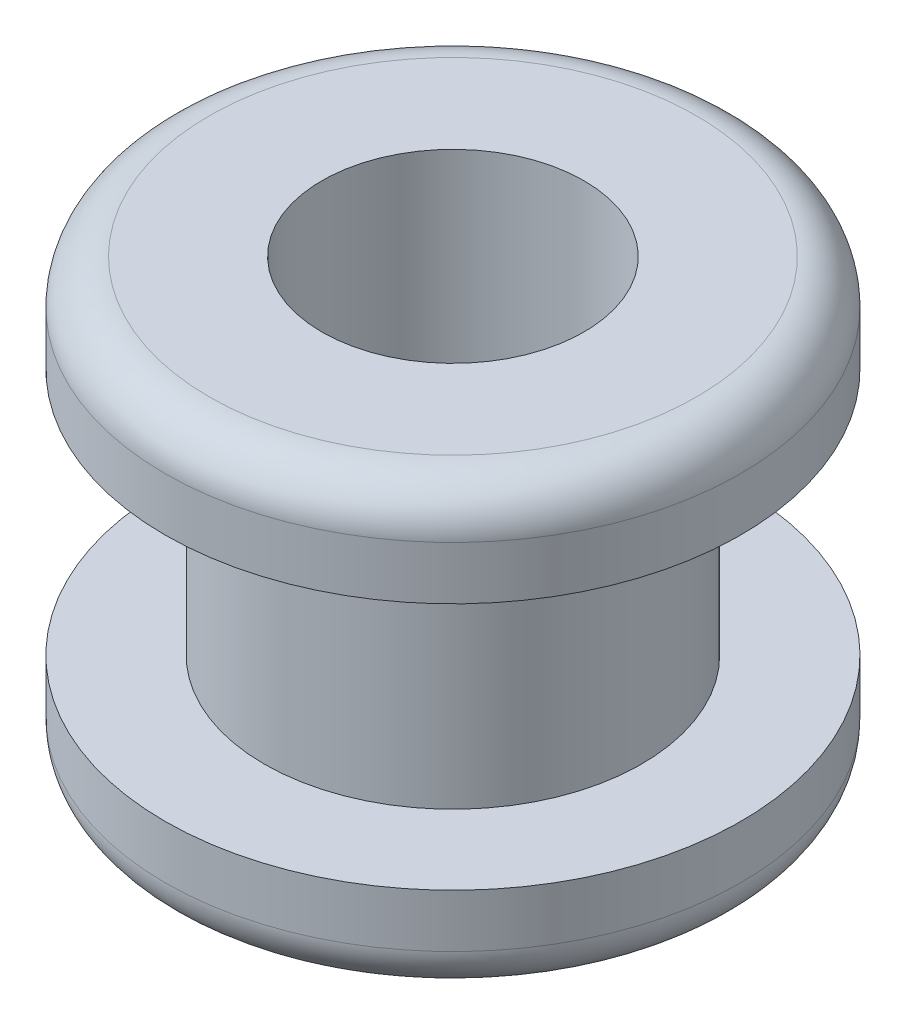
SolidWorks part; units mm, degrees
ref_plane "Ön Düzlem" through (0, 0, 0) normal (0, 0, 1) x (1, 0, 0)
ref_plane "Üst Düzlem" through (0, 0, 0) normal (0, 1, 0) x (1, 0, 0)
ref_plane "Sağ Düzlem" through (0, 0, 0) normal (1, 0, 0) x (0, 0, -1)
sketch "Çizim1" plane through (0, 0, 0) normal (1, 0, 0) x (0, 0, -1)
  line L0 (0, 5) -> (0, 0)
  line L1 (0, 5) -> (-1.27, 5)
  line L2 (1.48, 5) -> (1.48, 0.688) construction
  line L3 (-0.65, 3.9) -> (-0.65, 1.1)
  line L4 (-0.65, 3.9) -> (-1.77, 3.9)
  line L5 (-1.77, 3.9) -> (-1.77, 4.5)
  line L6 (-0.65, 1.1) -> (-1.77, 1.1)
  line L7 (-1.77, 1.1) -> (-1.77, 0.5)
  line L8 (0, 0) -> (-1.27, 0)
  arc A0 (-1.27, 5) -> (-1.77, 4.5) centre (-1.27, 4.5) ccw
  arc A1 (-1.27, 0) -> (-1.77, 0.5) centre (-1.27, 0.5) cw
  dimension "D1" = 1.48
  dimension "D2" = 2.8
revolve "Döndür1" add sketch "Çizim1" angle 360 about L2
